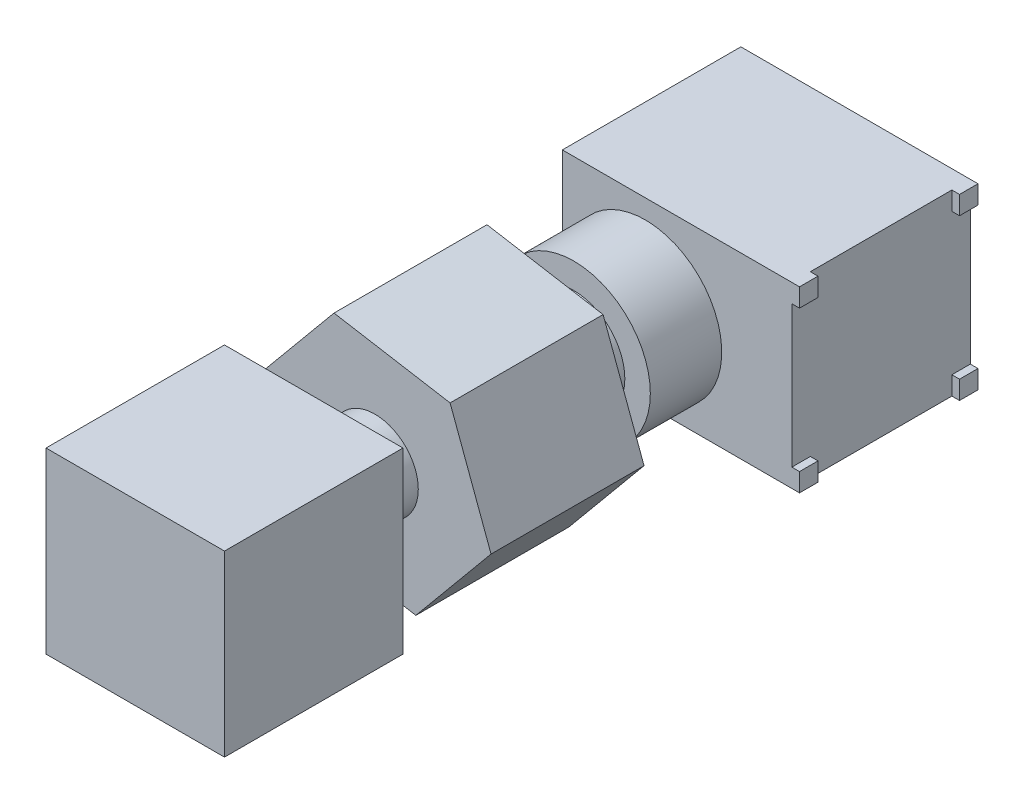
SolidWorks part; units mm, degrees
material "黄銅"
ref_plane "正面" through (0, 0, 0) normal (0, 0, 1) x (1, 0, 0)
ref_plane "平面" through (0, 0, 0) normal (0, 1, 0) x (1, 0, 0)
ref_plane "右側面" through (0, 0, 0) normal (1, 0, 0) x (0, 0, -1)
sketch "Sketch1" plane through (0, 0, 0) normal (0, 1, 0) x (1, 0, 0)
  line L1 (-4.5, 3.5) -> (4.5, 3.5)
  line L2 (-4.5, 3.5) -> (-4.5, -3.5)
  line L3 (-4.5, -3.5) -> (4.5, -3.5)
  line L4 (4.5, 3.5) -> (4.5, -3.5)
  line L5 (-4.5, 3.5) -> (4.5, -3.5) construction
  line L6 (-4.5, -3.5) -> (4.5, 3.5) construction
  point P0 (0, 0)
  dimension "D1" = 9
  dimension "D2" = 7
extrude "Boss-Extrude1" add sketch "Sketch1" along normal blind 7
sketch "Sketch4" plane through (4.5, 0, 0) normal (1, 0, 0) x (0, 0, -1)
  line L1 (-3.5, 7) -> (-2.775, 7)
  line L2 (-3.5, 7) -> (-3.5, 6.275)
  line L3 (-3.5, 6.275) -> (-2.775, 6.275)
  line L4 (-2.775, 7) -> (-2.775, 6.275)
  line L5 (3.5, 7) -> (2.775, 7)
  line L6 (3.5, 7) -> (3.5, 6.275)
  line L7 (3.5, 6.275) -> (2.775, 6.275)
  line L8 (2.775, 7) -> (2.775, 6.275)
  line L9 (-3.5, 0) -> (-2.775, 0)
  line L10 (-3.5, 0) -> (-3.5, 0.725)
  line L11 (-3.5, 0.725) -> (-2.775, 0.725)
  line L12 (-2.775, 0) -> (-2.775, 0.725)
  line L13 (3.5, 0) -> (2.775, 0)
  line L14 (3.5, 0) -> (3.5, 0.725)
  line L15 (3.5, 0.725) -> (2.775, 0.725)
  line L16 (2.775, 0) -> (2.775, 0.725)
  dimension "D1" = 0.725
  dimension "D2" = 0.725
  dimension "D3" = 0.725
  dimension "D4" = 0.725
  dimension "D5" = 0.725
  dimension "D6" = 0.725
  dimension "D7" = 0.725
  dimension "D8" = 0.725
extrude "Boss-Extrude3" add sketch "Sketch4" along normal blind 0.3
sketch "ｽｹｯﾁ1" plane through (0, 0, 3.5) normal (0, 0, 1) x (1, 0, 0)
  line L0 (-4.5, 0) -> (4.8, 0) construction
  line L1 (-4.5, 7) -> (-4.5, 0) construction
  circle A0 centre (-1.25, 3.25) radius 3
  dimension "D3" = 6
  dimension "D1" = 3.25
  dimension "D2" = 3.25
extrude "ﾎﾞｽ - 押し出し1" add sketch "ｽｹｯﾁ1" along normal blind 2.8
sketch "ｽｹｯﾁ2" plane through (0, 0, 6.3) normal (0, 0, 1) x (1, 0, 0)
  circle A0 centre (-1.25, 3.25) radius 2
extrude "ﾎﾞｽ - 押し出し2" add sketch "ｽｹｯﾁ2" along normal blind 1.8
sketch "ｽｹｯﾁ3" plane through (0, 0, 8.1) normal (0, 0, 1) x (1, 0, 0)
  line L1 (1.6979, 6.8058) -> (-2.8554, 7.5808)
  line L2 (-2.8554, 7.5808) -> (-5.8033, 4.025)
  line L3 (-5.8033, 4.025) -> (-4.1979, -0.3058)
  line L4 (-4.1979, -0.3058) -> (0.3554, -1.0808)
  line L5 (0.3554, -1.0808) -> (3.3033, 2.475)
  line L6 (3.3033, 2.475) -> (1.6979, 6.8058)
  circle A0 centre (-1.25, 3.25) radius 4 construction
  dimension "D1" = 4
extrude "ﾎﾞｽ - 押し出し3" add sketch "ｽｹｯﾁ3" along normal blind 6
sketch "ｽｹｯﾁ4" plane through (0, 0, 14.1) normal (0, 0, 1) x (1, 0, 0)
  line L0 (3.3033, 2.475) -> (1.6979, 6.8058) construction
  line L1 (-2.8554, 7.5808) -> (-5.8033, 4.025) construction
  circle A0 centre (-1.25, 3.25) radius 1.7
  dimension "D1" = 4
  dimension "D2" = 4
extrude "ﾎﾞｽ - 押し出し4" add sketch "ｽｹｯﾁ4" along normal blind 2.4
sketch "ｽｹｯﾁ5" plane through (0, 0, 16.5) normal (0, 0, 1) x (1, 0, 0)
  line L1 (-4.75, -0.25) -> (2.25, -0.25)
  line L2 (-4.75, -0.25) -> (-4.75, 6.75)
  line L3 (-4.75, 6.75) -> (2.25, 6.75)
  line L4 (2.25, -0.25) -> (2.25, 6.75)
  line L5 (-4.75, -0.25) -> (2.25, 6.75) construction
  line L6 (-4.75, 6.75) -> (2.25, -0.25) construction
  point P0 (-1.25, 3.25)
extrude "ﾎﾞｽ - 押し出し5" add sketch "ｽｹｯﾁ5" along normal blind 7
